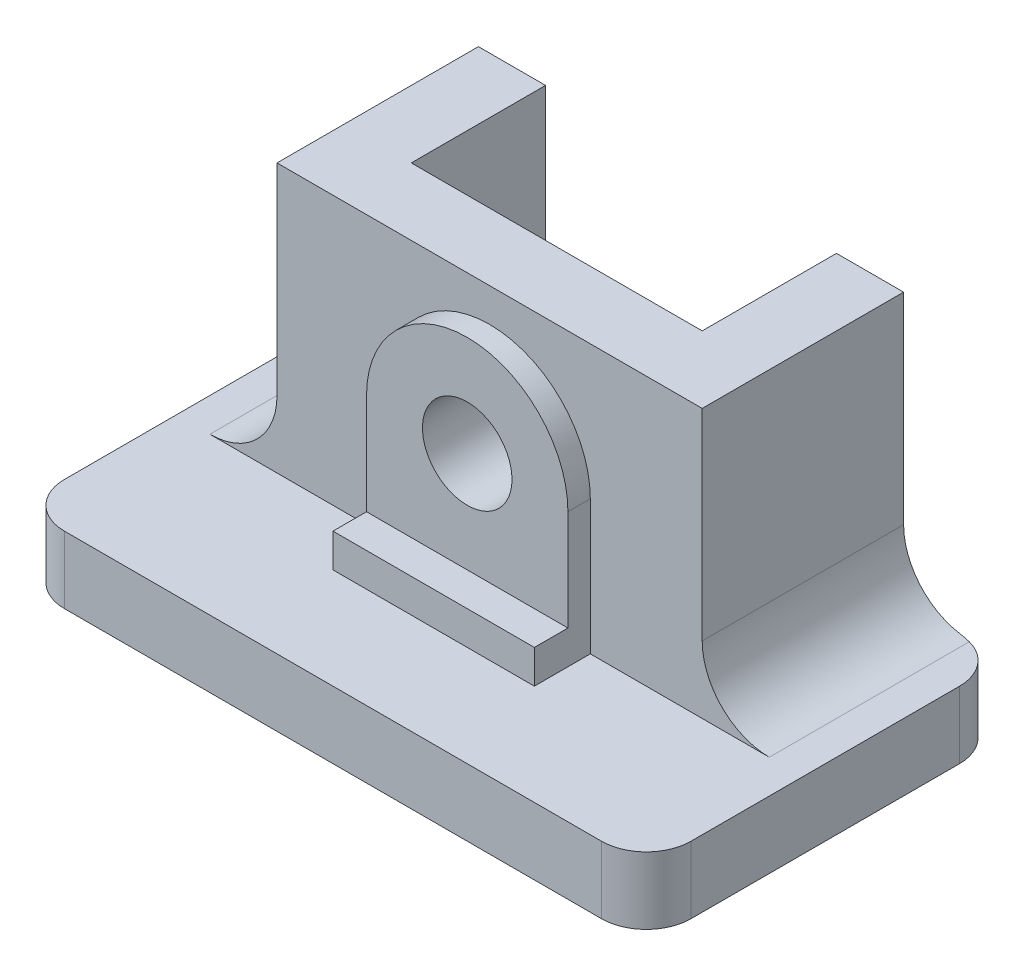
SolidWorks part; units mm, degrees
ref_plane "Front Plane" through (0, 0, 0) normal (0, 0, 1) x (1, 0, 0)
ref_plane "Top Plane" through (0, 0, 0) normal (0, 1, 0) x (1, 0, 0)
ref_plane "Right Plane" through (0, 0, 0) normal (1, 0, 0) x (0, 0, -1)
sketch "Sketch1" plane through (0, 0, 0) normal (0, 0, 1) x (1, 0, 0)
  line L0 (-44.45, 0) -> (-44.45, 47.625) construction
  line L1 (-88.9, 47.625) -> (0, 47.625)
  line L2 (-14.2875, 47.625) -> (-14.2875, 19.05)
  line L3 (-88.9, 0) -> (0, 0)
  line L4 (0, 47.625) -> (0, 0)
  line L5 (-4.7625, 9.525) -> (0, 9.525)
  line L6 (-84.1375, 9.525) -> (-88.9, 9.525)
  line L7 (-88.9, 47.625) -> (-88.9, 0)
  line L8 (-74.6125, 47.625) -> (-74.6125, 19.05)
  arc A0 (-14.2875, 19.05) -> (-4.7625, 9.525) centre (-4.7625, 19.05) ccw
  arc A1 (-74.6125, 19.05) -> (-84.1375, 9.525) centre (-84.1375, 19.05) cw
  point P9 (-14.2875, 9.525)
  point P17 (-74.6125, 9.525)
  dimension "D5" = 9.525
  dimension "D1" = 44.45
  dimension "D2" = 47.625
  dimension "D3" = 30.1625
  dimension "D4" = 38.1
extrude "Boss-Extrude1" add sketch "Sketch1" along normal blind 50.8 contours L3 L0 L1 L8 A1 L6 L7 | L0 L3 L4 L5 A0 L2 L1
sketch "Sketch2" plane through (0, 47.625, 0) normal (0, 1, 0) x (1, 0, 0)
  line L1 (-74.6125, 0) -> (-14.2875, 0) construction
  line L3 (-65.0875, 0) -> (-23.8125, 0)
  line L4 (-65.0875, 0) -> (-65.0875, -19.05)
  line L5 (-88.9, -50.8) -> (-88.9, 0) construction
  line L6 (-88.9, -28.575) -> (0, -28.575)
  line L7 (-88.9, -28.575) -> (-88.9, -50.8)
  line L8 (-88.9, -50.8) -> (0, -50.8)
  line L9 (0, -28.575) -> (0, -50.8)
  line L10 (-65.0875, -19.05) -> (-23.8125, -19.05)
  line L11 (-23.8125, 0) -> (-23.8125, -19.05)
  point P15 (-44.45, 0)
  point P16 (-44.45, 0)
  dimension "D1" = 28.575
  dimension "D2" = 41.275
  dimension "D3" = 19.05
extrude "Cut-Extrude2" cut sketch "Sketch2" against normal through all
sketch "Sketch3" plane through (0, 0, 28.575) normal (0, 0, 1) x (1, 0, 0)
  line L0 (-88.9, 0) -> (-44.45, 0)
  line L1 (0, 0) -> (-88.9, 0) construction
  line L2 (-44.45, 47.625) -> (-44.45, 0) construction
  line L3 (-14.2875, 47.625) -> (-74.6125, 47.625) construction
  line L4 (-88.9, 0) -> (-88.9, 9.525)
  line L5 (-88.9, 9.525) -> (0, 9.525)
  line L6 (-58.7375, 28.575) -> (-58.7375, 9.525)
  line L7 (-30.1625, 28.575) -> (-30.1625, 9.525)
  circle A0 centre (-44.45, 28.575) radius 6.35
  circle A1 centre (-44.45, 28.575) radius 14.2875
  point P21 (-44.45, 9.525)
  dimension "D1" = 12.7
  dimension "D3" = 28.575
  dimension "D2" = 19.05
extrude "Boss-Extrude2" add sketch "Sketch3" along normal blind 3.175 contours L2 A1 A0 | A1 L2 A0 | A1 L2 L5 L7 | L2 A1 L6 L5
sketch "Sketch4" plane through (0, 0, 28.575) normal (0, 0, 1) x (1, 0, 0)
  line L1 (-88.9, 0) -> (0, 0)
  line L2 (-88.9, 0) -> (-88.9, 9.525)
  line L3 (-88.9, 9.525) -> (0, 9.525)
  line L4 (0, 0) -> (0, 9.525)
extrude "Boss-Extrude3" add sketch "Sketch4" along normal blind 22.225
sketch "Sketch5" plane through (0, 0, 31.75) normal (0, 0, 1) x (1, 0, 0)
  line L0 (-30.1625, 28.575) -> (-30.1625, 9.525) construction
  line L1 (-58.7375, 9.525) -> (-30.1625, 9.525)
  line L2 (-58.7375, 9.525) -> (-58.7375, 14.2875)
  line L3 (-58.7375, 14.2875) -> (-30.1625, 14.2875)
  line L4 (-30.1625, 9.525) -> (-30.1625, 14.2875)
  circle A0 centre (-44.45, 28.575) radius 6.35 construction
  dimension "D1" = 14.2875
extrude "Boss-Extrude4" add sketch "Sketch5" along normal blind 4.7625
fillet "Fillet1" radius 6.35 4 edges at (-88.9, 4.7625, 0) (-88.9, 4.7625, 50.8) (0, 4.7625, 50.8) (0, 4.7625, 0)
sketch "Sketch6" plane through (0, 0, 28.575) normal (0, 0, 1) x (1, 0, 0)
  circle A0 centre (-44.45, 28.575) radius 6.35
  dimension "D1" = 12.7
extrude "Cut-Extrude3" cut sketch "Sketch6" against normal through all
